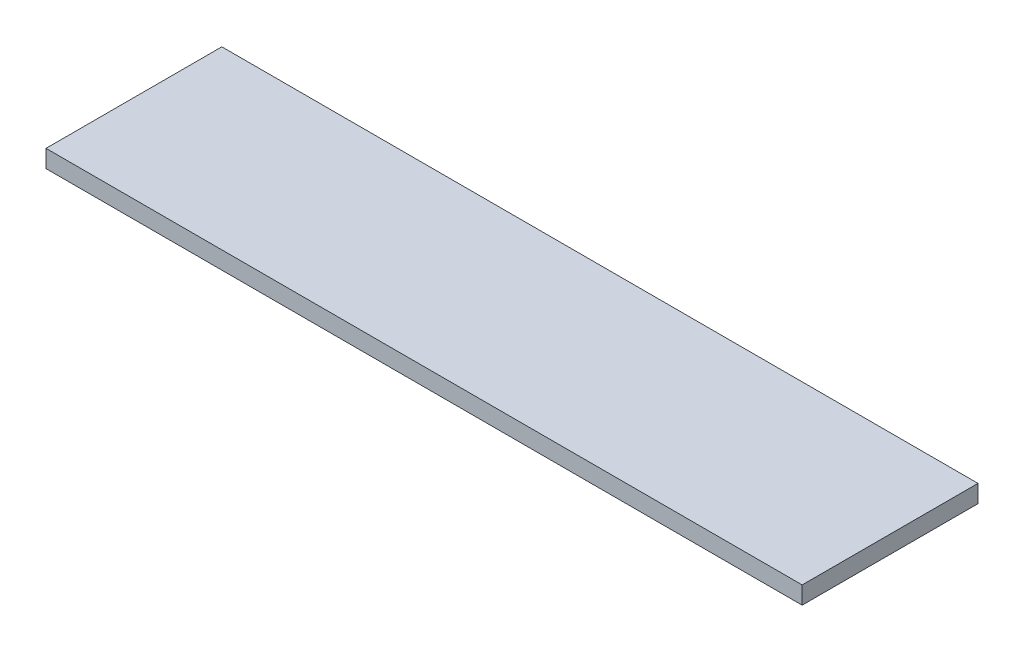
SolidWorks part; units mm, degrees
ref_plane "Front Plane" through (0, 0, 0) normal (0, 0, 1) x (1, 0, 0)
ref_plane "Top Plane" through (0, 0, 0) normal (0, 1, 0) x (1, 0, 0)
ref_plane "Right Plane" through (0, 0, 0) normal (1, 0, 0) x (0, 0, -1)
sketch "Sketch1" plane through (0, 0, 0) normal (0, 1, 0) x (1, 0, 0)
  line L0 (-215, 50) -> (215, -50) construction
  line L1 (-215, 50) -> (215, 50)
  line L2 (-215, 50) -> (-215, -50)
  line L3 (-215, -50) -> (215, -50)
  line L4 (215, 50) -> (215, -50)
  dimension "D1" = 430
  dimension "D2" = 100
extrude "Boss-Extrude1" add sketch "Sketch1" along normal blind 10
